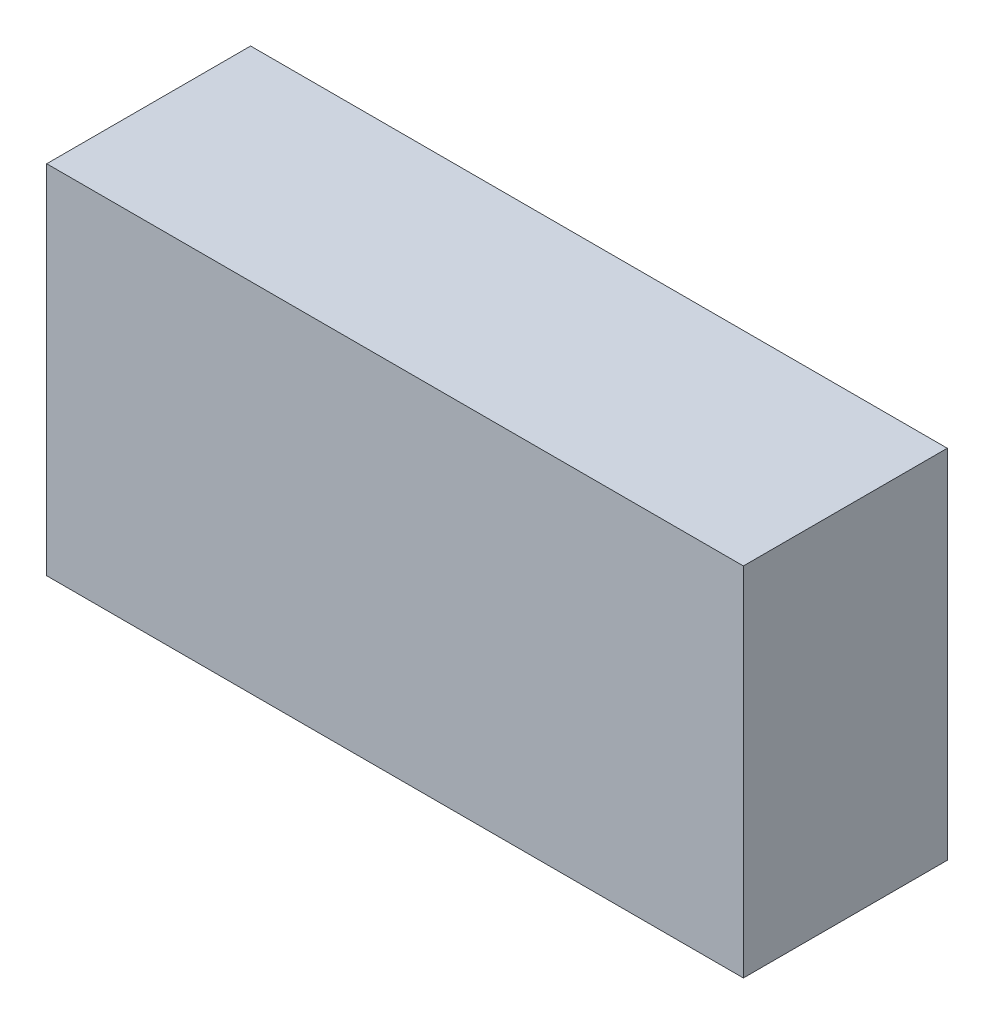
SolidWorks part; units mm, degrees
ref_plane "Front Plane" through (0, 0, 0) normal (0, 0, 1) x (1, 0, 0)
ref_plane "Top Plane" through (0, 0, 0) normal (0, 1, 0) x (1, 0, 0)
ref_plane "Right Plane" through (0, 0, 0) normal (1, 0, 0) x (0, 0, -1)
sketch "Sketch2" plane through (0, 0, 0) normal (0, 0, 1) x (1, 0, 0)
  line L1 (0, 0) -> (41, 0)
  line L2 (0, 0) -> (0, 21)
  line L3 (0, 21) -> (41, 21)
  line L4 (41, 0) -> (41, 21)
  dimension "D1" = 41
  dimension "D2" = 21
extrude "Boss-Extrude1" add sketch "Sketch2" along normal blind 12
